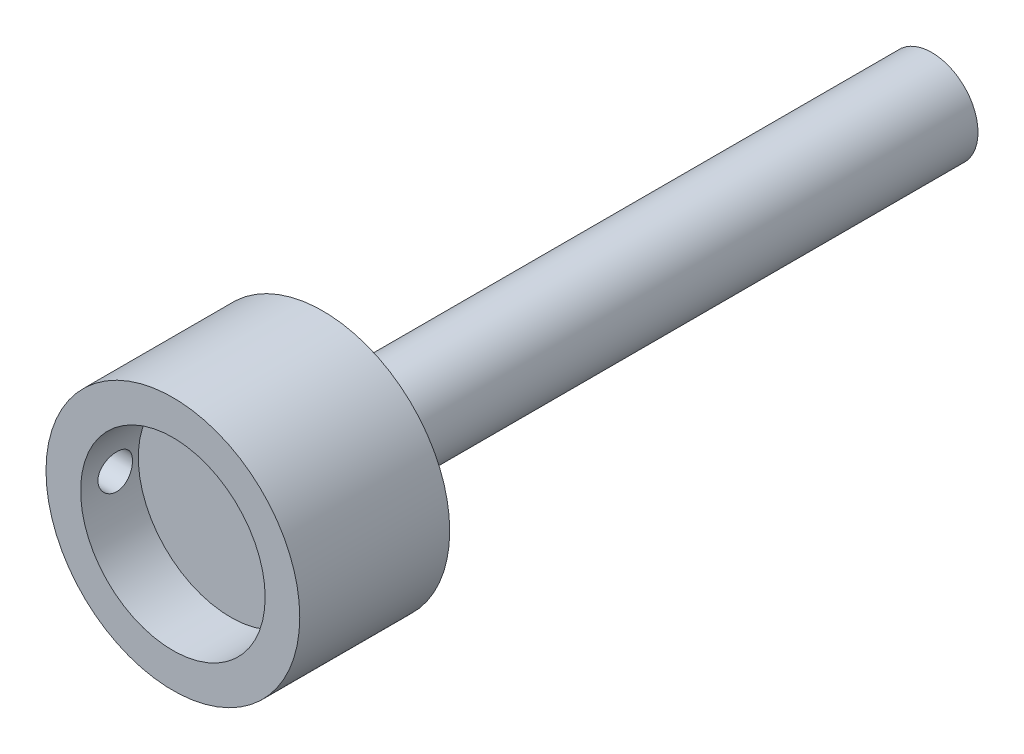
SolidWorks part; units mm, degrees
ref_plane "Alzado" through (0, 0, 0) normal (0, 0, 1) x (1, 0, 0)
ref_plane "Planta" through (0, 0, 0) normal (0, 1, 0) x (1, 0, 0)
ref_plane "Vista lateral" through (0, 0, 0) normal (1, 0, 0) x (0, 0, -1)
sketch "Croquis1" plane through (0, 0, 0) normal (0, 0, 1) x (1, 0, 0)
  circle A0 centre (0, 0) radius 11
  dimension "D1" = 22
extrude "Saliente-Extruir1" add sketch "Croquis1" along normal blind 13
sketch "Croquis2" plane through (0, 0, 13) normal (0, 0, 1) x (1, 0, 0)
  circle A0 centre (0, 0) radius 8
  dimension "D1" = 16
extrude "Cortar-Extruir1" cut sketch "Croquis2" against normal blind 5
sketch "Croquis3" plane through (0, 0, 0) normal (1, 0, 0) x (0, 0, -1)
  line L1 (-10, 0) -> (0, 0) construction
  line L2 (0, -11) -> (0, 11) construction
  circle A0 centre (-10, 0) radius 1.5
  dimension "D2" = 3
  dimension "D1" = 10
extrude "Cortar-Extruir2" cut sketch "Croquis3" against normal blind 15
sketch "Croquis4" plane through (0, 0, 0) normal (0, 0, -1) x (-1, 0, 0)
  circle A0 centre (0, 0) radius 4
  dimension "D1" = 8
extrude "Saliente-Extruir2" add sketch "Croquis4" along normal blind 52.8
